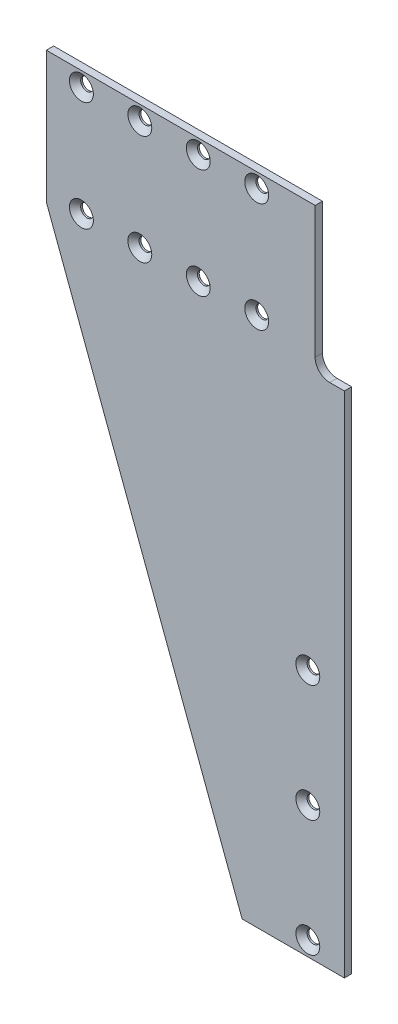
SolidWorks part; units mm, degrees
material "ASTM A36 Steel"
ref_plane "Front Plane" through (0, 0, 0) normal (0, 0, 1) x (1, 0, 0)
ref_plane "Top Plane" through (0, 0, 0) normal (0, 1, 0) x (1, 0, 0)
ref_plane "Right Plane" through (0, 0, 0) normal (1, 0, 0) x (0, 0, -1)
sketch "Sketch1" plane through (0, 0, 0) normal (0, 0, 1) x (1, 0, 0)
  line L0 (0, 0) -> (0, 220.98)
  line L1 (-12.7, 284.48) -> (-129.54, 284.48)
  line L2 (-129.54, 284.48) -> (-129.54, 227.33)
  line L3 (-129.54, 227.33) -> (-44.45, 0)
  line L4 (-44.45, 0) -> (0, 0)
  line L5 (-12.7, 284.48) -> (-12.7, 227.33)
  line L6 (-6.35, 220.98) -> (0, 220.98)
  arc A0 (-12.7, 227.33) -> (-6.35, 220.98) centre (-6.35, 227.33) ccw
  point P11 (-12.7, 220.98)
  dimension "D7" = 6.35
  dimension "D1" = 44.45
  dimension "D2" = 284.48
  dimension "D3" = 129.54
  dimension "D4" = 57.15
  dimension "D5" = 12.7
  dimension "D6" = 220.98
extrude "Boss-Extrude1" add sketch "Sketch1" against normal blind 3.175
sketch "Sketch2" plane through (0, 0, 0) normal (0, 0, 1) x (1, 0, 0)
  line L0 (-114.3, 278.13) -> (-38.1, 278.13) construction
  line L1 (-114.3, 230.505) -> (-38.1, 230.505) construction
  line L2 (-12.7, 284.48) -> (-129.54, 284.48) construction
  line L3 (-15.875, 6.35) -> (-15.875, 57.15) construction
  line L4 (-15.875, 57.15) -> (-15.875, 107.95) construction
  line L5 (-44.45, 0) -> (0, 0) construction
  line L6 (0, 0) -> (0, 220.98) construction
  line L7 (-12.7, 227.33) -> (-12.7, 284.48) construction
  dimension "D1" = 47.625
  dimension "D2" = 6.35
  dimension "D3" = 50.8
  dimension "D4" = 50.8
  dimension "D5" = 6.35
  dimension "D6" = 15.875
  dimension "D7" = 76.2
  dimension "D8" = 25.4
hole_wizard "CSK for #0 Flat Head Machine Screw (100)1" positions "3DSketch1" profile "Sketch3" countersink size "#0" standard "ANSI Inch" end condition through all
sketch3d "3DSketch1"
  point P0 (-114.3, 278.13, 0)
  point P3 (-114.3, 230.505, 0)
sketch "Sketch3" plane through (-114.3, 278.13, 0) normal (1, 0, 0) x (0, -1, 0)
  line L0 (0, 0) -> (0, 3.175)
  line L1 (0, 3.175) -> (2.7559, 3.175)
  line L2 (2.7559, 3.175) -> (2.7559, 2.4384)
  line L3 (2.7559, 2.4384) -> (5.1943, 0)
  line L5 (5.1943, 0) -> (0, 0)
  line L6 (-2.7559, 2.4384) -> (-5.1943, 0) construction
  line L11 (0, -6.35) -> (0, 107.95) construction
  dimension "Thru Hole Dia." = 5.5118
  dimension "Thru Hole Depth" = 3.175
  dimension "Near C'Sink Dia." = 10.3886
  dimension "Near C'Sink Angle" = 90
pattern_linear "LPattern1" count 4 spacing 25.4 along (1, 0, 0) of "CSK for #0 Flat Head Machine Screw (100)1"
hole_wizard "CSK for #0 Flat Head Machine Screw (100)2" positions "3DSketch2" profile "Sketch4" countersink size "#0" standard "ANSI Inch" end condition through all
sketch3d "3DSketch2"
  point P0 (-15.875, 107.95, 0)
sketch "Sketch4" plane through (-15.875, 107.95, 0) normal (1, 0, 0) x (0, -1, 0)
  line L0 (0, 0) -> (0, 3.175)
  line L1 (0, 3.175) -> (2.7559, 3.175)
  line L2 (2.7559, 3.175) -> (2.7559, 2.4384)
  line L3 (2.7559, 2.4384) -> (5.1943, 0)
  line L5 (5.1943, 0) -> (0, 0)
  line L6 (-2.7559, 2.4384) -> (-5.1943, 0) construction
  line L11 (0, -6.35) -> (0, 107.95) construction
  dimension "Thru Hole Dia." = 5.5118
  dimension "Thru Hole Depth" = 3.175
  dimension "Near C'Sink Dia." = 10.3886
  dimension "Near C'Sink Angle" = 90
pattern_linear "LPattern2" count 3 spacing 50.8 along (0, -1, 0) of "CSK for #0 Flat Head Machine Screw (100)2"
